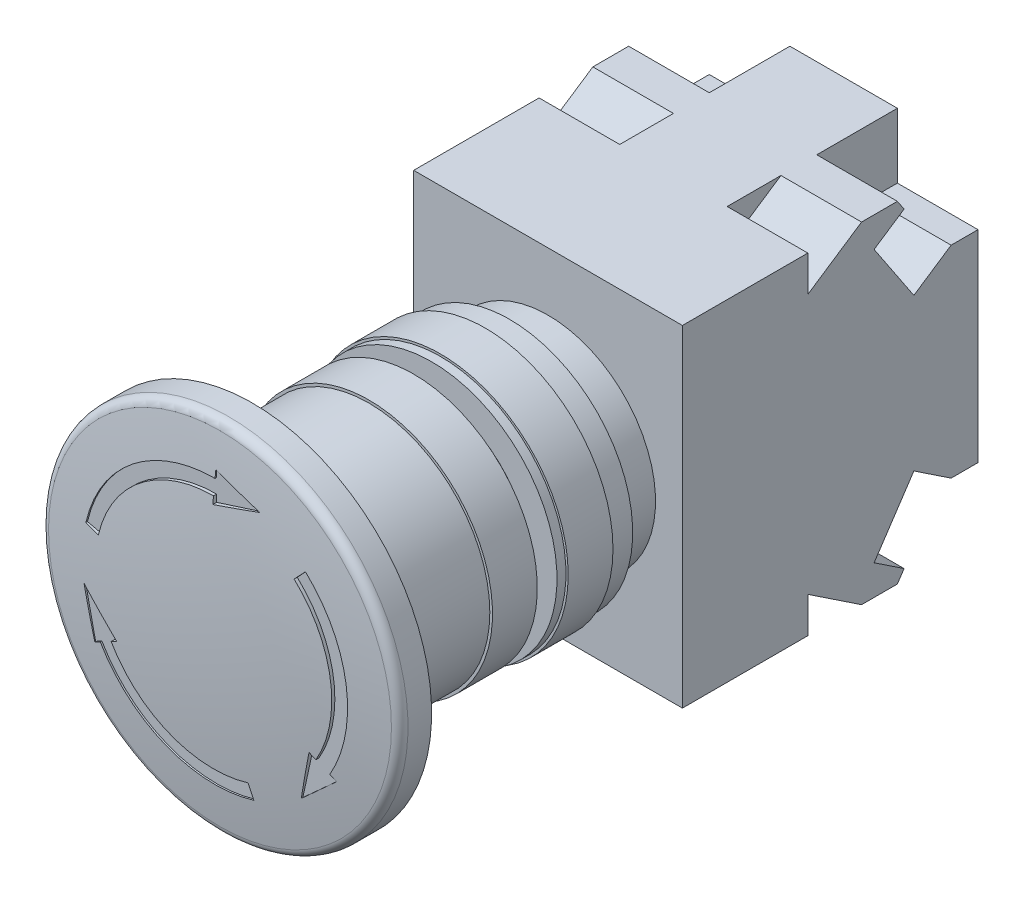
SolidWorks part; units mm, degrees
material "ABS"
ref_plane "Plan de face" through (0, 0, 0) normal (0, 0, 1) x (1, 0, 0)
ref_plane "Plan de dessus" through (0, 0, 0) normal (0, 1, 0) x (1, 0, 0)
ref_plane "Plan de droite" through (0, 0, 0) normal (1, 0, 0) x (0, 0, -1)
ref_axis "Axe1" through (0, 0, -56.84) along (0, 0, 1)
sketch "Esquisse1" plane through (0, 0, 0) normal (1, 0, 0) x (0, 0, -1)
  line L0 (0, 18.5) -> (0, -18.5)
  line L1 (0, -18.5) -> (-33, -18.5)
  line L2 (-33, -18.5) -> (-33, 18.5)
  line L3 (-33, 18.5) -> (0, 18.5)
  dimension "D1" = 37
  dimension "D2" = 33
extrude "Boss.-Extru.1" add sketch "Esquisse1" along normal mid plane 30
sketch "Esquisse2" plane through (15, 0, 0) normal (1, 0, 0) x (0, 0, -1)
  line L0 (-9, -18.5) -> (-8.2516, -17.3774)
  line L1 (-33, -18.5) -> (0, -18.5) construction
  line L2 (-8.2516, -17.3774) -> (-11.5979, -15.1466)
  line L3 (-11.5979, -15.1466) -> (-7.1603, -8.4902)
  line L4 (-7.1603, -8.4902) -> (-3, -11.2637)
  line L5 (-3, -11.2637) -> (0, -11.2637)
  line L6 (0, -18.5) -> (0, 18.5) construction
  line L7 (0, -11.2637) -> (0, -20.6032)
  line L8 (-19, -20.6032) -> (0, -20.6032)
  line L9 (0, 0) -> (-33, 0) construction
  line L10 (-13, -18.5) -> (-19, -14.5)
  line L11 (-19, -14.5) -> (-19, -18.5)
  line L12 (-19, -18.5) -> (-19, -20.6032)
  line L13 (-19, 20.6032) -> (0, 20.6032)
  line L15 (-13, -18.5) -> (-9, -18.5)
  line L16 (-33, 18.5) -> (-33, -18.5) construction
  line L17 (-13, 18.5) -> (-9, 18.5)
  line L20 (-19, 18.5) -> (-19, 20.6032)
  line L21 (-19, 14.5) -> (-19, 18.5)
  line L22 (-13, 18.5) -> (-19, 14.5)
  line L24 (0, 11.2637) -> (0, 20.6032)
  line L25 (-3, 11.2637) -> (0, 11.2637)
  line L26 (-7.1603, 8.4902) -> (-3, 11.2637)
  line L27 (-11.5979, 15.1466) -> (-7.1603, 8.4902)
  line L28 (-8.2516, 17.3774) -> (-11.5979, 15.1466)
  line L29 (-9, 18.5) -> (-8.2516, 17.3774)
  dimension "D1" = 6
  dimension "D2" = 14
  dimension "D3" = 4
  dimension "D4" = 3
  dimension "D5" = 8
  dimension "D6" = 4
  dimension "D7" = 5
  dimension "D8" = 4.0217
extrude "Enlèv. mat.-Extru.1" cut sketch "Esquisse2" against normal blind 9
sketch "Esquisse3" plane through (-15, 0, 0) normal (-1, 0, 0) x (0, 0, 1)
  line L0 (-2.985, 11.2637) -> (3, 11.2637)
  line L1 (3, 11.2637) -> (7.1603, 8.4902)
  line L2 (7.1603, 8.4902) -> (11.5979, 15.1466)
  line L3 (11.5979, 15.1466) -> (8.2516, 17.3774)
  line L4 (8.2516, 17.3774) -> (9, 18.5)
  line L5 (9, 18.5) -> (13, 18.5)
  line L6 (13, 18.5) -> (19, 14.5)
  line L7 (19, 14.5) -> (19, 18.5)
  line L8 (19, 18.5) -> (21.5041, 22.2561)
  line L9 (21.5041, 22.2561) -> (-2.985, 22.2561)
  line L10 (-2.985, 22.2561) -> (-2.985, 11.2637)
  line L11 (0, 0) -> (33, 0) construction
  line L12 (33, 18.5) -> (33, -18.5) construction
  line L13 (-2.985, -22.2561) -> (-2.985, -11.2637)
  line L14 (21.5041, -22.2561) -> (-2.985, -22.2561)
  line L15 (19, -18.5) -> (21.5041, -22.2561)
  line L16 (19, -14.5) -> (19, -18.5)
  line L17 (13, -18.5) -> (19, -14.5)
  line L18 (9, -18.5) -> (13, -18.5)
  line L19 (8.2516, -17.3774) -> (9, -18.5)
  line L20 (11.5979, -15.1466) -> (8.2516, -17.3774)
  line L21 (7.1603, -8.4902) -> (11.5979, -15.1466)
  line L22 (3, -11.2637) -> (7.1603, -8.4902)
  line L23 (-2.985, -11.2637) -> (3, -11.2637)
extrude "Enlèv. mat.-Extru.2" cut sketch "Esquisse3" against normal blind 9
sketch "Esquisse4" plane through (0, 0, 33) normal (0, 0, 1) x (1, 0, 0)
  circle A0 centre (0, 0) radius 12
  dimension "D1" = 24
extrude "Boss.-Extru.2" add sketch "Esquisse4" along normal blind 8
sketch "Esquisse5" plane through (0, 0, 41) normal (0, 0, 1) x (1, 0, 0)
  circle A0 centre (0, 0) radius 11
  dimension "D1" = 22
extrude "Boss.-Extru.3" add sketch "Esquisse5" along normal blind 8.5
sketch "Esquisse6" plane through (0, 0, 49.5) normal (0, 0, 1) x (1, 0, 0)
  circle A0 centre (0, 0) radius 7.775
  dimension "D1" = 15.55
extrude "Boss.-Extru.4" add sketch "Esquisse6" along normal blind 5.8
sketch "Esquisse7" plane through (0, 0, 55.3) normal (0, 0, 1) x (1, 0, 0)
  circle A0 centre (0, 0) radius 10
  dimension "D1" = 20
extrude "Boss.-Extru.5" add sketch "Esquisse7" along normal blind 4
sketch "Esquisse8" plane through (0, 0, 59.3) normal (0, 0, 1) x (1, 0, 0)
  circle A0 centre (0, 0) radius 8.5
  dimension "D1" = 17
extrude "Boss.-Extru.6" add sketch "Esquisse8" along normal blind 5
sketch "Esquisse9" plane through (0, 0, 0) normal (1, 0, 0) x (0, 0, -1)
  line L0 (-45, 12) -> (-37.3, 12)
  line L1 (-37.3, 12) -> (-37.3, 13.75)
  line L2 (-37.3, 13.75) -> (-40, 13.75)
  line L3 (-40, 13.75) -> (-40, 14.25)
  line L4 (-40, 14.25) -> (-45, 14.25)
  line L5 (-45, 14.25) -> (-45, 12)
  line L7 (-33, 12) -> (-41, 12) construction
  line L8 (-33, 12) -> (-33, -12) construction
  dimension "D1" = 7.7
  dimension "D2" = 5
  dimension "D3" = 12
  dimension "D4" = 0.5
  dimension "D5" = 14.25
revolve "Révolution1" add sketch "Esquisse9" angle 360 about axis through (0, 0, -56.84) along (0, 0, 1)
sketch "Esquisse10" plane through (0, 0, 0) normal (1, 0, 0) x (0, 0, -1)
  line L0 (-45, 14.25) -> (-45, -14.25) construction
  line L1 (-45, 14) -> (-46, 14)
  line L2 (-45, 14) -> (-45, 11)
  line L3 (-45, 11) -> (-46, 11)
  line L4 (-46, 14) -> (-46, 11)
  line L5 (-41, 11) -> (-49.5, 11) construction
  dimension "D1" = 14
  dimension "D2" = 1
revolve "Révolution2" add sketch "Esquisse10" angle 360 about axis through (0, 0, -56.84) along (0, 0, 1)
sketch "Esquisse11" plane through (0, 0, 0) normal (1, 0, 0) x (0, 0, -1)
  line L0 (-48, 11) -> (-48, 13.8)
  line L1 (-41, 11) -> (-49.5, 11) construction
  line L2 (-48, 13.8) -> (-53, 13.8)
  line L3 (-53, 13.8) -> (-53, 13.5)
  line L4 (-53, 13.5) -> (-62, 13.5)
  line L5 (-62, 13.5) -> (-62, 11)
  line L6 (-62, 11) -> (-48, 11)
  line L7 (-33, 18.5) -> (-33, -18.5) construction
  dimension "D1" = 14
  dimension "D2" = 5
  dimension "D3" = 15
  dimension "D4" = 13.5
  dimension "D5" = 13.8
revolve "Révolution3" add sketch "Esquisse11" angle 360 about axis through (0, 0, -56.84) along (0, 0, 1)
sketch "Esquisse12" plane through (0, 0, 0) normal (1, 0, 0) x (0, 0, -1)
  line L0 (-69.5, 11.25) -> (-60.5, 11.25)
  line L1 (-60.5, 11.25) -> (-60.5, 8.5)
  line L2 (-60.5, 8.5) -> (-69.5, 8.5)
  line L3 (-69.5, 8.5) -> (-69.5, 0)
  line L4 (-69.5, 0) -> (-71, 0)
  line L5 (-71, 0) -> (-69.5, 20) construction
  line L6 (-69.5, 20) -> (-66, 20)
  line L7 (-66, 20) -> (-66, 18.5)
  line L8 (-66, 18.5) -> (-68.5, 18.5)
  line L9 (-68.5, 18.5) -> (-69.5, 11.25) construction
  line L10 (-71, 0) -> (-71, 20) construction
  line L11 (-33, 18.5) -> (-33, -18.5) construction
  line L12 (-69.5, 11.25) -> (-69.5, 20) construction
  line L13 (-33, 12) -> (-33, -12) construction
  arc A0 (-69.5, 20) -> (-71, 0) centre (63.0833, 0) ccw
  arc A1 (-68.5, 18.5) -> (-69.5, 11.25) centre (-42.7187, 11.25) ccw
  dimension "D1" = 11.25
  dimension "D2" = 1.5
  dimension "D3" = 2.5
  dimension "D4" = 9
  dimension "D5" = 5.5
  dimension "D6" = 3.5
  dimension "D7" = 20
  dimension "D8" = 33
  dimension "D9" = 38
revolve "Révolution4" add sketch "Esquisse12" angle 360 about axis through (0, 0, -56.84) along (0, 0, 1)
fillet "Congé1" radius 1 2 edges at (-18.5, 0, 68.5) (-20, 0, 69.5)
ref_plane "Plan1" through (0, 0, 71) normal (0, 0, 1) x (1, 0, 0)
sketch "Esquisse13" plane through (0, 0, 71) normal (0, 0, 1) x (1, 0, 0)
  line L0 (0, 15.6) -> (0, 14.8)
  line L1 (0, 12.4) -> (5, 14)
  line L2 (5, 14) -> (0, 15.6)
  line L3 (0, 14) -> (5, 14) construction
  line L4 (9.0006, 9.6555) -> (10.0916, 10.8258)
  line L5 (10.7387, -6.2) -> (9.6244, -11.3301)
  line L6 (13.51, -7.8) -> (12.8172, -7.4)
  line L7 (9.6244, -11.3301) -> (13.51, -7.8)
  line L8 (3.8616, -12.6225) -> (4.3296, -14.1525)
  line L9 (-10.7387, -6.2) -> (-14.6244, -2.6699)
  line L10 (-13.51, -7.8) -> (-12.8172, -7.4)
  line L11 (-14.6244, -2.6699) -> (-13.51, -7.8)
  line L12 (-12.8622, 2.967) -> (-14.4213, 3.3267)
  line L13 (11.4315, -6.6) -> (10.7387, -6.2)
  line L14 (-11.4315, -6.6) -> (-10.7387, -6.2)
  line L15 (0, 13.2) -> (0, 12.4)
  circle A0 centre (0, 0) radius 14 construction
  arc A1 (-12.8172, -7.4) -> (4.3296, -14.1525) centre (0, 0) ccw
  arc A2 (-11.4315, -6.6) -> (3.8616, -12.6225) centre (0, 0) ccw
  arc A3 (0, 13.2) -> (-12.8622, 2.967) centre (0, 0) ccw
  circle A4 centre (0, 0) radius 14.8 construction
  circle A5 centre (0, 0) radius 13.2 construction
  arc A6 (0, 14.8) -> (-14.4213, 3.3267) centre (0, 0) ccw
  arc A7 (4.896, 13.9667) -> (4.8, 14) centre (0, 0) ccw
  arc A8 (11.4315, -6.6) -> (9.0006, 9.6555) centre (0, 0) ccw
  arc A9 (12.8172, -7.4) -> (10.0916, 10.8258) centre (0, 0) ccw
  point P4 (12.6232, 3.8593)
  point P13 (14.1533, 4.3271)
  point P25 (0, 0)
  dimension "D3" = 28
  dimension "D4" = 3.2
  dimension "D5" = 5
  dimension "D6" = 6
  dimension "D1" = 0.8
  dimension "D2" = 0.8
  dimension "D7" = 3
extrude "Enlèv. mat.-Extru.3" cut sketch "Esquisse13" against normal blind 1
